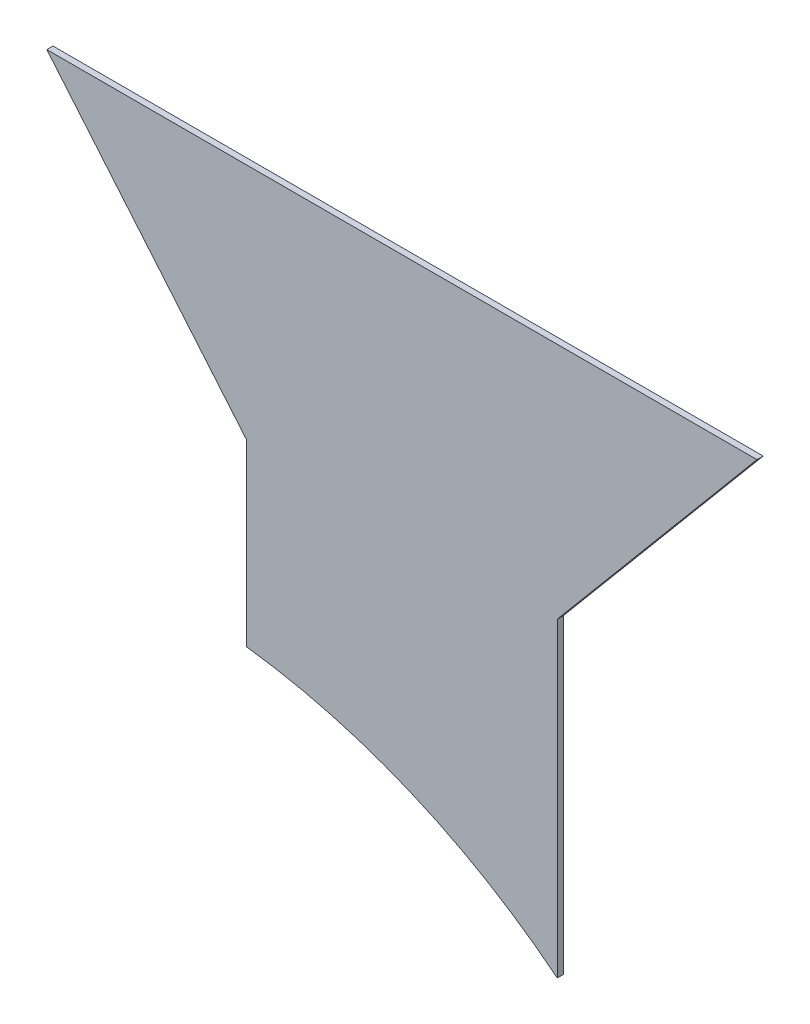
SolidWorks part; units mm, degrees
material "Plain Carbon Steel"
ref_plane "Front Plane" through (0, 0, 0) normal (0, 0, 1) x (1, 0, 0)
ref_plane "Top Plane" through (0, 0, 0) normal (0, 1, 0) x (1, 0, 0)
ref_plane "Right Plane" through (0, 0, 0) normal (1, 0, 0) x (0, 0, -1)
sketch "Sketch1" plane through (0, 0, 0) normal (0, 0, 1) x (1, 0, 0)
  line L1 (38.1, 0) -> (38.1, 76.2)
  line L2 (38.1, 76.2) -> (87.0804, 134.5726)
  line L6 (0, 0) -> (38.1, 0) construction
  line L7 (0, 0) -> (0, 134.5726) construction
  line L8 (-87.0804, 134.5726) -> (87.0804, 134.5726)
  line L9 (-38.1, 32.2375) -> (-38.1, 76.2)
  line L10 (-38.1, 76.2) -> (-87.0804, 134.5726)
  line L11 (0, 0) -> (0, -123.071) construction
  line L12 (-57.15, -118.9672) -> (24.7773, -118.9672) construction
  line L13 (-38.1, 0) -> (-38.1, 32.2375) construction
  line L14 (-38.1, 0) -> (0, 0) construction
  line L15 (-38.1, 32.2375) -> (-38.1, -118.9672) construction
  line L16 (38.1, 0) -> (38.1, -109.3889) construction
  arc A1 (38.1, 0) -> (-38.1, 32.2375) centre (-57.15, -118.9672) ccw
  circle A2 centre (-57.15, -118.9672) radius 152.4 construction
  dimension "D5" = 152.4
  dimension "D6" = 95.25
  dimension "D1" = 38.1
  dimension "D2" = 140
  dimension "D3" = 76.2
  dimension "D4" = 76.2
extrude "Funnel - Side Panel" add sketch "Sketch1" along normal blind 1.5189
